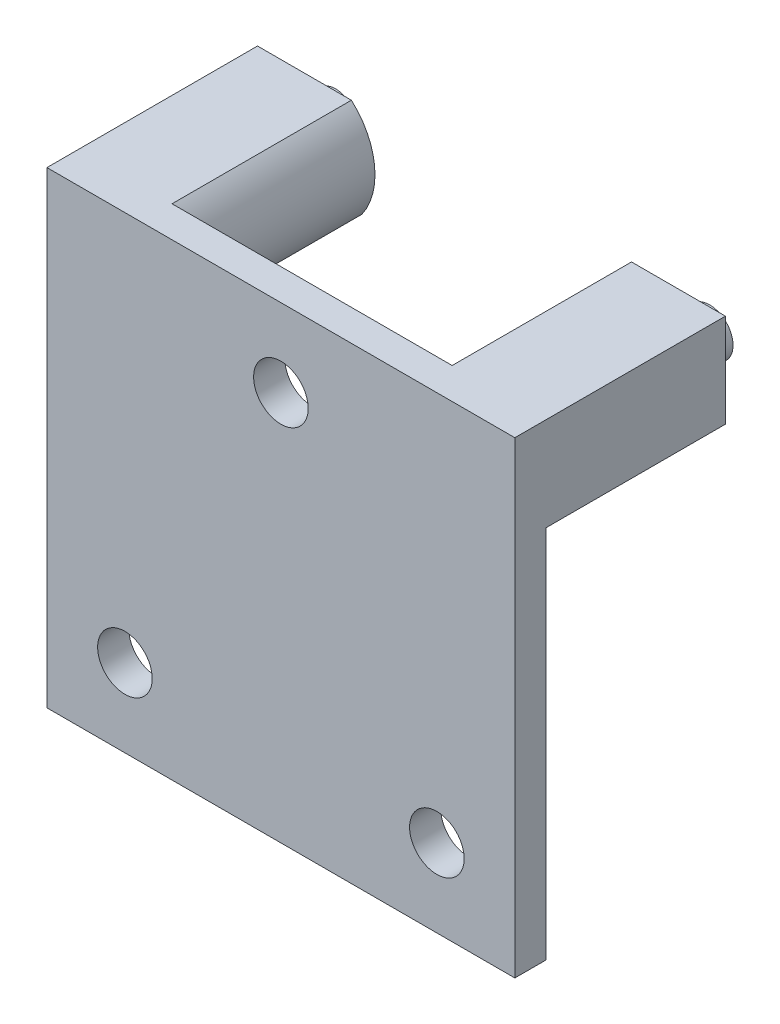
SolidWorks part; units mm, degrees
ref_plane "Front Plane" through (0, 0, 0) normal (0, 0, 1) x (1, 0, 0)
ref_plane "Top Plane" through (0, 0, 0) normal (0, 1, 0) x (1, 0, 0)
ref_plane "Right Plane" through (0, 0, 0) normal (1, 0, 0) x (0, 0, -1)
sketch "Sketch1" plane through (0, 0, 0) normal (0, 0, 1) x (1, 0, 0)
  line L0 (15, 0) -> (14.9802, 18.25) construction
  line L1 (5.5, 0) -> (24.5, 0) construction
  line L3 (29.9901, -5.875) -> (-0.0099, -5.875)
  line L4 (29.9901, -5.875) -> (29.9901, 24.125)
  line L5 (29.9901, 24.125) -> (-0.0099, 24.125)
  line L6 (-0.0099, -5.875) -> (-0.0099, 24.125)
  line L7 (29.9901, -5.875) -> (-0.0099, 24.125) construction
  line L8 (29.9901, 24.125) -> (-0.0099, -5.875) construction
  arc A0 (3.6035, 23.75) -> (26.3614, 23.7406) centre (14.9862, 32.7787) ccw construction
  point P7 (14.9901, 9.125)
  dimension "D1" = 30
  dimension "D2" = 30
extrude "Boss-Extrude1" add sketch "Sketch1" along normal blind 2
sketch "Sketch2" plane through (0, 0, 0) normal (0, 0, -1) x (-1, 0, 0)
  line L0 (-14.9901, 24.125) -> (-14.9901, -5.875) construction
  line L1 (-29.9901, 24.125) -> (0.0099, 24.125) construction
  line L2 (0.0099, -5.875) -> (-29.9901, -5.875) construction
  line L3 (0.0099, 24.125) -> (0.0099, 18.125)
  line L4 (0.0099, 24.125) -> (0.0099, -5.875) construction
  line L5 (0.0099, 24.125) -> (-6.0099, 24.125)
  line L6 (0.0099, 18.125) -> (-6.6824, 18.125)
  arc A0 (-6.0099, 24.125) -> (-6.6824, 18.125) centre (-3, 20.75) ccw
  dimension "D1" = 6
extrude "Boss-Extrude3" add sketch "Sketch2" along normal up to vertex (11.5 mm away)
sketch "Sketch3" plane through (0, 0, -11.5) normal (0, 0, -1) x (-1, 0, 0)
  circle A0 centre (-3, 20.75) radius 1.5
  arc A1 (-6.0099, 24.125) -> (-6.6824, 18.125) centre (-3, 20.75) ccw construction
  dimension "D1" = 3
extrude "Boss-Extrude4" add sketch "Sketch3" along normal blind 2
ref_plane "Plane1" through (14.9901, 0, 0) normal (1, 0, 0) x (0, 0, -1)
mirror "Mirror1" about plane through (14.9901, 0, 0) normal (1, 0, 0) of "Boss-Extrude4", "Boss-Extrude3"
sketch "Sketch4" plane through (0, 0, 0) normal (0, 0, -1) x (-1, 0, 0)
  circle A0 centre (-13.708, 3.465) radius 3.5
  circle A1 centre (-13.708, 3.465) radius 5
  circle A2 centre (-13.708, 3.465) radius 3.25 construction
  dimension "D1" = 0.25
  dimension "D2" = 1.5
extrude "Boss-Extrude5" add sketch "Sketch4" along normal blind 5
sketch "Sketch5" plane through (0, 0, 0) normal (0, 0, -1) x (-1, 0, 0)
  line L0 (-14.9901, 24.125) -> (-14.9901, -5.875) construction
  line L1 (-23.9702, 24.125) -> (-6.0099, 24.125) construction
  line L2 (0.0099, -5.875) -> (-29.9901, -5.875) construction
  line L3 (-14.9901, 9.125) -> (-29.9901, 9.125) construction
  line L4 (-29.9901, -5.875) -> (-29.9901, 18.125) construction
  circle A0 centre (-24.9901, -0.875) radius 1.75
  circle A1 centre (-4.9901, -0.875) radius 1.75
  circle A2 centre (-14.9901, 19.125) radius 1.75
  dimension "D1" = 3.5
  dimension "D2" = 10
  dimension "D3" = 10
  dimension "D4" = 10
extrude "Cut-Extrude1" cut sketch "Sketch5" against normal through all
